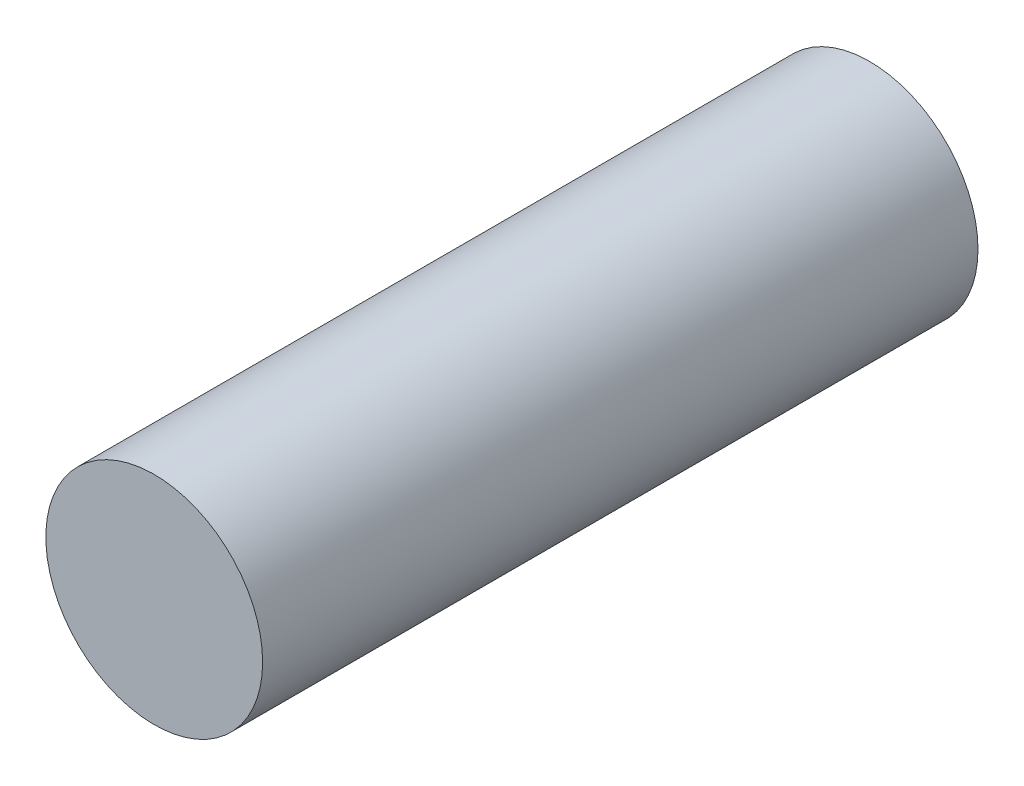
SolidWorks part; units mm, degrees
ref_plane "Front Plane" through (0, 0, 0) normal (0, 0, 1) x (1, 0, 0)
ref_plane "Top Plane" through (0, 0, 0) normal (0, 1, 0) x (1, 0, 0)
ref_plane "Right Plane" through (0, 0, 0) normal (1, 0, 0) x (0, 0, -1)
sketch "Sketch1" plane through (0, 0, 0) normal (0, 0, 1) x (1, 0, 0)
  circle A0 centre (0, 0) radius 6.35
  dimension "D1" = 12.7
extrude "Boss-Extrude1" add sketch "Sketch1" along normal blind 41.91
